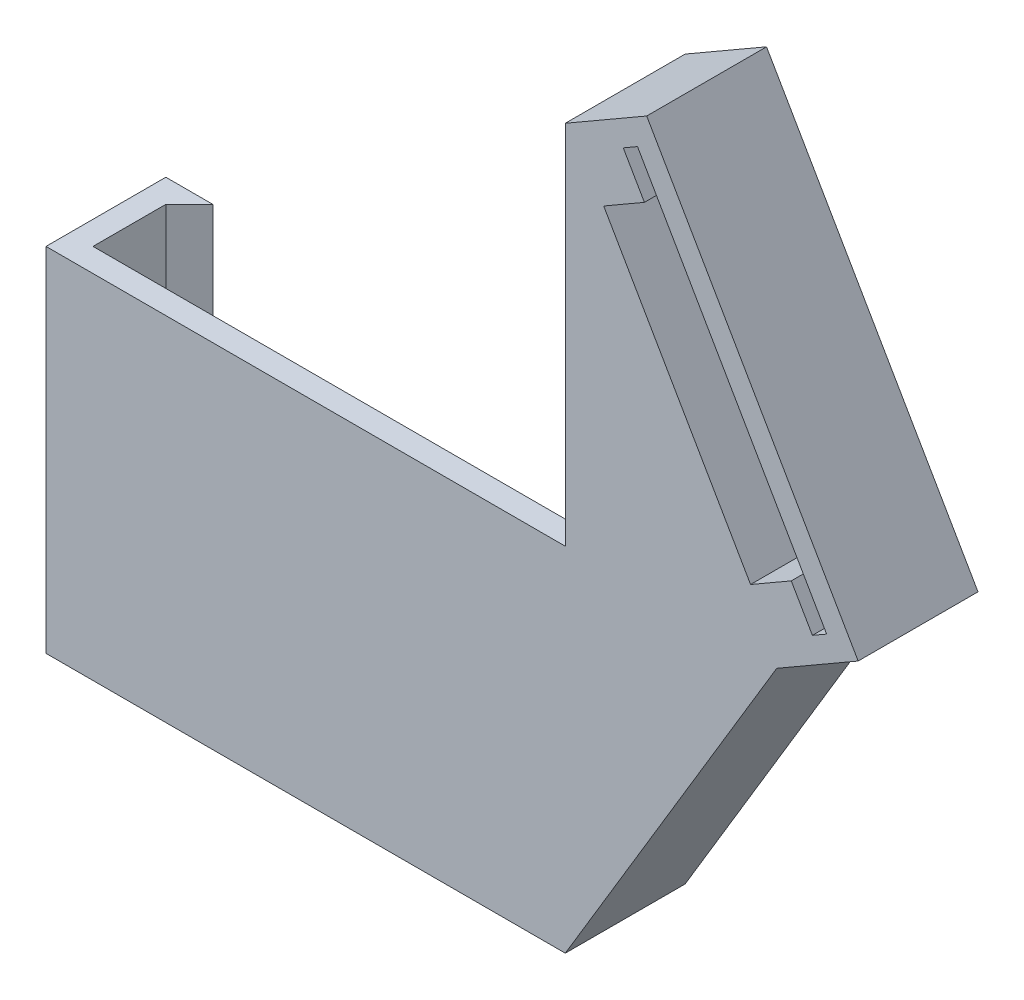
SolidWorks part; units mm, degrees
ref_plane "Front Plane" through (0, 0, 0) normal (0, 0, 1) x (1, 0, 0)
ref_plane "Top Plane" through (0, 0, 0) normal (0, 1, 0) x (1, 0, 0)
ref_plane "Right Plane" through (0, 0, 0) normal (1, 0, 0) x (0, 0, -1)
sketch "Sketch1" plane through (0, 0, 0) normal (0, 1, 0) x (1, 0, 0)
  line L0 (18.1, 3.1) -> (18.1, 5.1)
  line L1 (20.1, -3.1) -> (-20.1, -3.1)
  line L2 (20.1, -3.1) -> (20.1, 3.1)
  line L3 (20.1, 3.1) -> (18.1, 3.1)
  line L4 (-20.1, -3.1) -> (-20.1, 3.1)
  line L5 (20.1, -3.1) -> (-20.1, 3.1) construction
  line L6 (20.1, 3.1) -> (-20.1, -3.1) construction
  line L7 (18.1, 5.1) -> (22.1, 5.1)
  line L8 (22.1, 5.1) -> (22.1, -5.1)
  line L9 (22.1, -5.1) -> (-22.1, -5.1)
  line L10 (-22.1, -5.1) -> (-22.1, 5.1)
  line L11 (-22.1, 5.1) -> (-18.1, 5.1)
  line L12 (-18.1, 5.1) -> (-20.1, 3.1)
  point P0 (0, 0)
  dimension "D1" = 40.2
  dimension "D2" = 6.2
  dimension "D3" = 2
  dimension "D4" = 2
  dimension "D5" = 45
  dimension "D6" = 2
  dimension "D7" = 2
  dimension "D8" = 2
extrude "Boss-Extrude1" add sketch "Sketch1" along normal blind 30
sketch "Sketch2" plane through (0, 0, 5.1) normal (0, 0, 1) x (1, 0, 0)
  line L0 (47.0282, 34) -> (29.0282, 65.1769)
  line L5 (47.0282, 34) -> (40.1, 30)
  line L6 (29.0282, 65.1769) -> (22.1, 61.1769)
  line L8 (47.0282, 34) -> (22.1, 61.1769) construction
  line L9 (29.0282, 65.1769) -> (40.1, 30) construction
  line L11 (40.1, 30) -> (22.1, 0)
  line L12 (22.1, 0) -> (22.1, 30)
  line L13 (40.1, 30) -> (22.1, 30) construction
  line L14 (22.1, 30) -> (22.1, 61.1769)
  point P1 (34.5641, 47.5885)
  dimension "D1" = 30
  dimension "D2" = 36
  dimension "D3" = 8
extrude "Boss-Extrude2" add sketch "Sketch2" against normal up to surface (10.2 mm away) up to face at (20.1, 15, -5.1)
sketch "Sketch3" plane through (0, 0, 5.1) normal (0, 0, 1) x (1, 0, 0)
  line L0 (44.3462, 34.6454) -> (28.2462, 62.5315)
  line L1 (44.3462, 34.6454) -> (43.1337, 33.9454)
  line L2 (28.2462, 62.5315) -> (27.0337, 61.8315)
  line L3 (43.1337, 33.9454) -> (41.3337, 37.0631)
  line L4 (44.3462, 34.6454) -> (27.0337, 61.8315) construction
  line L5 (28.2462, 62.5315) -> (43.1337, 33.9454) construction
  line L6 (47.0282, 34) -> (29.0282, 65.1769) construction
  line L7 (35.6899, 48.2385) -> (38.0282, 49.5885) construction
  line L9 (28.8337, 58.7138) -> (25.3696, 56.7138)
  line L10 (41.3337, 37.0631) -> (37.8696, 35.0631)
  line L11 (25.3696, 56.7138) -> (37.8696, 35.0631)
  line L12 (28.8337, 58.7138) -> (27.0337, 61.8315)
  line L13 (35.6899, 48.2385) -> (31.6196, 45.8885) construction
  point P1 (35.6899, 48.2385)
  dimension "D1" = 2
  dimension "D2" = 1.4
  dimension "D3" = 32.2
  dimension "D4" = 25
  dimension "D5" = 4
extrude "Cut-Extrude1" cut sketch "Sketch3" against normal up to surface (10.2 mm away) up to face at (27.3321, 31.2942, -5.1)
